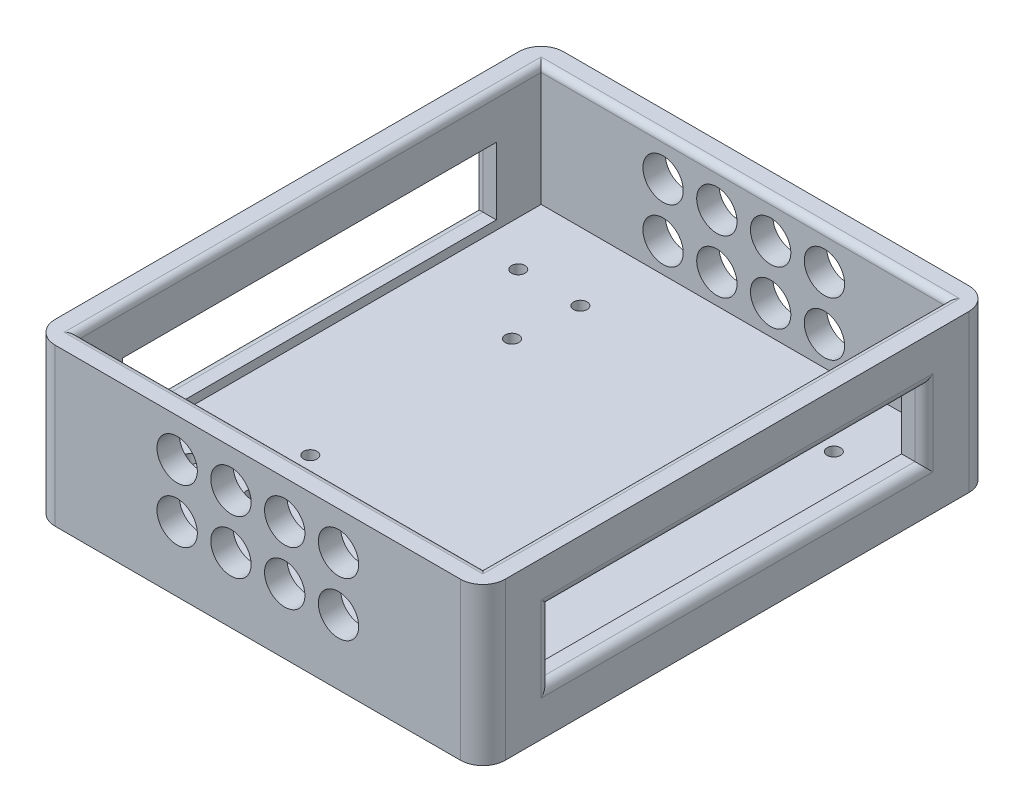
SolidWorks part; units mm, degrees
ref_plane "Front Plane" through (0, 0, 0) normal (0, 0, 1) x (1, 0, 0)
ref_plane "Top Plane" through (0, 0, 0) normal (0, 1, 0) x (1, 0, 0)
ref_plane "Right Plane" through (0, 0, 0) normal (1, 0, 0) x (0, 0, -1)
sketch "Sketch1" plane through (0, 0, 0) normal (0, 1, 0) x (1, 0, 0)
  line L1 (-50.2, -56.7) -> (50.2, -56.7)
  line L2 (-50.2, -56.7) -> (-50.2, 56.7)
  line L3 (-50.2, 56.7) -> (50.2, 56.7)
  line L4 (50.2, -56.7) -> (50.2, 56.7)
  line L5 (-50.2, -56.7) -> (50.2, 56.7) construction
  line L6 (-50.2, 56.7) -> (50.2, -56.7) construction
  point P0 (0, 0)
  dimension "D1" = 100.4
  dimension "D2" = 113.4
extrude "Boss-Extrude2" add sketch "Sketch1" along normal blind 35 contours L3 L4 L1 L2
sketch "Sketch2" plane through (0, 35, 0) normal (0, 1, 0) x (1, 0, 0)
  line L1 (-45.2, -51.7) -> (45.2, -51.7)
  line L2 (-45.2, -51.7) -> (-45.2, 51.7)
  line L3 (-45.2, 51.7) -> (45.2, 51.7)
  line L4 (45.2, -51.7) -> (45.2, 51.7)
  line L5 (-45.2, -51.7) -> (45.2, 51.7) construction
  line L6 (-45.2, 51.7) -> (45.2, -51.7) construction
  point P0 (0, 0)
  dimension "D1" = 103.4
  dimension "D2" = 90.4
extrude "Cut-Extrude1" cut sketch "Sketch2" against normal blind 27
fillet "Fillet4" radius 5 4 edges at (50.2, 17.5, -56.7) (-50.2, 17.5, -56.7) (-50.2, 17.5, 56.7) (50.2, 17.5, 56.7)
sketch "Sketch3" plane through (0, 0, -56.7) normal (0, 0, -1) x (-1, 0, 0)
  line L0 (45.2, 0) -> (-45.2, 0) construction
  line L1 (-50.2, 0) -> (-50.2, 35) construction
  circle A0 centre (-18, 14.5) radius 4.5
  dimension "D1" = 14.5
  dimension "D3" = 9
  dimension "D2" = 32.2
sketch "Sketch4" plane through (50.2, 0, 0) normal (1, 0, 0) x (0, 0, -1)
  line L0 (-56.7, 0) -> (-56.7, 35) construction
  line L1 (-41.7, 25) -> (41.7, 25)
  line L2 (-41.7, 25) -> (-41.7, 10)
  line L3 (-41.7, 10) -> (41.7, 10)
  line L4 (41.7, 25) -> (41.7, 10)
  line L6 (-51.7, 0) -> (51.7, 0) construction
  dimension "D1" = 83.4
  dimension "D2" = 15
  dimension "D3" = 10
  dimension "D4" = 15
extrude "Cut-Extrude3" cut sketch "Sketch4" against normal blind 123
fillet "Fillet5" radius 2 4 edges at (50.2, 17.5, 41.7) (50.2, 25, 0) (50.2, 17.5, -41.7) (50.2, 10, 0)
fillet "Fillet6" radius 2 4 edges at (-50.2, 17.5, 41.7) (-50.2, 25, 0) (-50.2, 17.5, -41.7) (-50.2, 10, 0)
extrude "Cut-Extrude4" cut sketch "Sketch3" against normal blind 123 contours A0
sketch "Sketch5" plane through (0, 8, 0) normal (0, 1, 0) x (1, 0, 0)
  line L0 (-50.2, -51.7) -> (-50.2, 51.7) construction
  line L1 (-45.2, -56.7) -> (45.2, -56.7) construction
  circle A0 centre (-22.5, 22.5) radius 1.5
  circle A1 centre (22.5, 22.5) radius 1.5
  circle A2 centre (-22.5, -22.5) radius 1.5
  circle A3 centre (22.5, -22.5) radius 1.5
  dimension "D1" = 45
  dimension "D2" = 45
  dimension "D3" = 45
  dimension "D4" = 45
  dimension "D5" = 27.7
  dimension "D6" = 34.2
extrude "Cut-Extrude5" cut sketch "Sketch5" against normal blind 37
sketch "Sketch6" plane through (0, 0, 0) normal (0, -1, 0) x (1, 0, 0)
  circle A0 centre (-22.5, 22.5) radius 3
  circle A1 centre (-22.5, -22.5) radius 3
  circle A2 centre (22.5, 22.5) radius 3
  circle A3 centre (22.5, -22.5) radius 3
extrude "Cut-Extrude6" cut sketch "Sketch6" against normal blind 4
sketch "Sketch7" plane through (0, 0, 0) normal (0, -1, 0) x (1, 0, 0)
  line L0 (-45.2, 56.7) -> (45.2, 56.7) construction
  line L1 (50.2, 51.7) -> (50.2, -51.7) construction
  line L2 (-45.2, 56.7) -> (45.2, 56.7) construction
  circle A0 centre (-21.25, 36.5) radius 1.5
  circle A1 centre (-21.25, -36.5) radius 1.5
  circle A2 centre (21.25, -36.5) radius 1.5
  circle A3 centre (21.25, 36.5) radius 1.5
  dimension "D1" = 42.5
  dimension "D8" = 20.2
  dimension "D9" = 3
  dimension "D10" = 3
  dimension "D11" = 3
  dimension "D12" = 3
  dimension "D2" = 42.5
  dimension "D3" = 73
  dimension "D4" = 73
  dimension "D5" = 20.2
  dimension "D6" = 28.95
  dimension "D7" = 28.95
extrude "Cut-Extrude7" cut sketch "Sketch7" against normal blind 17
sketch "Sketch8" plane through (0, 8, 0) normal (0, 1, 0) x (1, 0, 0)
  line L0 (-45.2, -56.7) -> (45.2, -56.7) construction
  line L1 (-50.2, -51.7) -> (-50.2, 51.7) construction
  circle A0 centre (-35.2, 36.6) radius 1.5
  circle A1 centre (35.2, 36.6) radius 1.5
  circle A2 centre (-35.2, -36.7) radius 1.5
  circle A3 centre (35.2, -36.7) radius 1.5
  dimension "D1" = 73.3
  dimension "D2" = 73.3
  dimension "D3" = 70.4
  dimension "D4" = 70.4
  dimension "D5" = 20
  dimension "D6" = 15
extrude "Cut-Extrude8" cut sketch "Sketch8" against normal blind 9
sketch "Sketch9" plane through (0, 0, 0) normal (0, -1, 0) x (1, 0, 0)
  circle A0 centre (-35.2, 36.7) radius 3
  circle A1 centre (35.2, 36.7) radius 3
  circle A2 centre (-35.2, -36.6) radius 3
  circle A3 centre (35.2, -36.6) radius 3
extrude "Cut-Extrude9" cut sketch "Sketch9" against normal blind 4
pattern_linear "LPattern2" count 4 spacing 12 along (-1, 0, 0) count 2 spacing 12 along (0, 1, 0) of "Cut-Extrude4"
fillet "Fillet7" radius 1.5 4 edges at (0, 35, 51.7) (45.2, 35, 0) (0, 35, -51.7) (-45.2, 35, 0)
